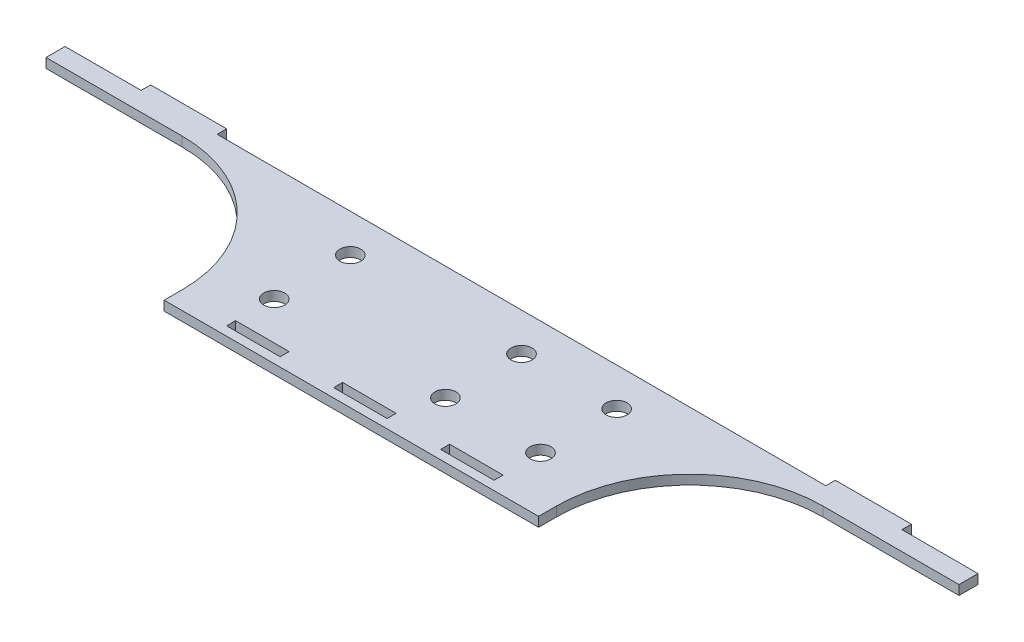
SolidWorks part; units mm, degrees
ref_plane "Front Plane" through (0, 0, 0) normal (0, 0, 1) x (1, 0, 0)
ref_plane "Top Plane" through (0, 0, 0) normal (0, 1, 0) x (1, 0, 0)
ref_plane "Right Plane" through (0, 0, 0) normal (1, 0, 0) x (0, 0, -1)
sketch "Sketch1" plane through (0, 0, 0) normal (0, 1, 0) x (1, 0, 0)
  line L0 (-106.95, 19.05) -> (-152.4, 19.05)
  line L1 (-152.4, -25.4) -> (152.4, -25.4)
  line L2 (-152.4, -25.4) -> (-152.4, 25.4)
  line L3 (-152.4, 25.4) -> (152.4, 25.4)
  line L4 (152.4, -25.4) -> (152.4, 25.4)
  line L5 (-152.4, -25.4) -> (152.4, 25.4) construction
  line L6 (-152.4, 25.4) -> (152.4, -25.4) construction
  line L7 (152.4, 19.05) -> (106.95, 19.05)
  line L8 (44.45, 12.7) -> (12.7, 12.7) construction
  line L9 (-44.45, -12.7) -> (44.45, -12.7) construction
  line L10 (-44.45, -12.7) -> (-44.45, 12.7) construction
  line L11 (-44.45, 12.7) -> (44.45, 12.7) construction
  line L12 (44.45, -12.7) -> (44.45, 12.7) construction
  line L13 (-44.45, -12.7) -> (44.45, 12.7) construction
  line L14 (-44.45, 12.7) -> (44.45, -12.7) construction
  line L15 (127, 28.575) -> (152.4, 28.575) construction
  line L20 (-127, 28.575) -> (-101.6, 28.575)
  line L21 (-127, 28.575) -> (-127, 25.4)
  line L22 (-127, 25.4) -> (-101.6, 25.4)
  line L23 (-101.6, 28.575) -> (-101.6, 25.4)
  line L24 (101.6, 28.575) -> (127, 28.575)
  line L25 (101.6, 28.575) -> (101.6, 25.4)
  line L26 (101.6, 25.4) -> (127, 25.4)
  line L27 (127, 28.575) -> (127, 25.4)
  line L28 (-127, 28.575) -> (-152.4, 28.575) construction
  line L29 (-26.7857, -28.4) -> (-8.9286, -28.4) construction
  line L34 (-62.5, -31.4) -> (62.5, -31.4)
  line L35 (-62.5, -31.4) -> (-62.5, -25.4)
  line L36 (-62.5, -25.4) -> (62.5, -25.4)
  line L37 (62.5, -31.4) -> (62.5, -25.4)
  line L38 (-62.5, -31.4) -> (62.5, -25.4) construction
  line L39 (-62.5, -25.4) -> (62.5, -31.4) construction
  line L40 (-44.6429, -28.4) -> (-26.7857, -28.4)
  line L41 (-44.6429, -28.4) -> (-44.6429, -25.4)
  line L42 (-44.6429, -25.4) -> (-26.7857, -25.4)
  line L43 (-26.7857, -28.4) -> (-26.7857, -25.4)
  line L44 (-44.6429, -28.4) -> (-26.7857, -25.4) construction
  line L45 (-44.6429, -25.4) -> (-26.7857, -28.4) construction
  line L46 (26.7857, -28.4) -> (44.6429, -28.4)
  line L47 (26.7857, -28.4) -> (26.7857, -25.4)
  line L48 (26.7857, -25.4) -> (44.6429, -25.4)
  line L49 (44.6429, -28.4) -> (44.6429, -25.4)
  line L50 (26.7857, -28.4) -> (44.6429, -25.4) construction
  line L51 (26.7857, -25.4) -> (44.6429, -28.4) construction
  line L52 (-8.9286, -28.4) -> (8.9286, -28.4)
  line L53 (-8.9286, -28.4) -> (-8.9286, -25.4)
  line L54 (-8.9286, -25.4) -> (8.9286, -25.4)
  line L55 (8.9286, -28.4) -> (8.9286, -25.4)
  line L56 (-8.9286, -28.4) -> (8.9286, -25.4) construction
  line L57 (-8.9286, -25.4) -> (8.9286, -28.4) construction
  line L58 (8.9286, -28.4) -> (26.7857, -28.4) construction
  line L59 (-44.6429, -28.4) -> (-26.7857, -28.4) construction
  line L60 (44.6429, -28.4) -> (62.5, -28.4) construction
  arc A0 (-106.95, 19.05) -> (-62.5, -25.4) centre (-106.95, -25.4) cw
  arc A1 (106.95, 19.05) -> (62.5, -25.4) centre (106.95, -25.4) ccw
  circle A2 centre (-44.45, 12.7) radius 3.5
  circle A3 centre (-44.45, -12.7) radius 3.5
  circle A4 centre (44.45, 12.7) radius 3.5
  circle A5 centre (44.45, -12.7) radius 3.5
  circle A6 centre (12.7, 12.7) radius 3.5
  circle A7 centre (12.7, -12.7) radius 3.5
  point P0 (0, 0)
  point P14 (0, 0)
  point P27 (0, -28.4)
  point P28 (35.7143, -26.9)
  point P40 (-35.7143, -26.9)
  point P46 (62.5, -41.9029)
  point P51 (0, -26.9)
  point P56 (0, 0)
  dimension "D4" = 44.45
  dimension "D8" = 7
  dimension "D9" = 7
  dimension "D1" = 50.8
  dimension "D2" = 304.8
  dimension "D3" = 125
  dimension "D5" = 88.9
  dimension "D6" = 25.4
  dimension "D7" = 31.75
  dimension "D10" = 6
  dimension "D11" = 3
  dimension "D12" = 25.4
  dimension "D13" = 3.175
extrude "Boss-Extrude1" add sketch "Sketch1" along normal blind 3.175 contours A1 L7 L4 L3 L2 L0 A0 L1 L36 A7 A6 A5 A4 A3 A2 | L55 L52 L53 L1 L43 L40 L41 L35 L34 L37 L49 L46 L47 | L23 L20 L21 L3 | L27 L24 L25 L3
